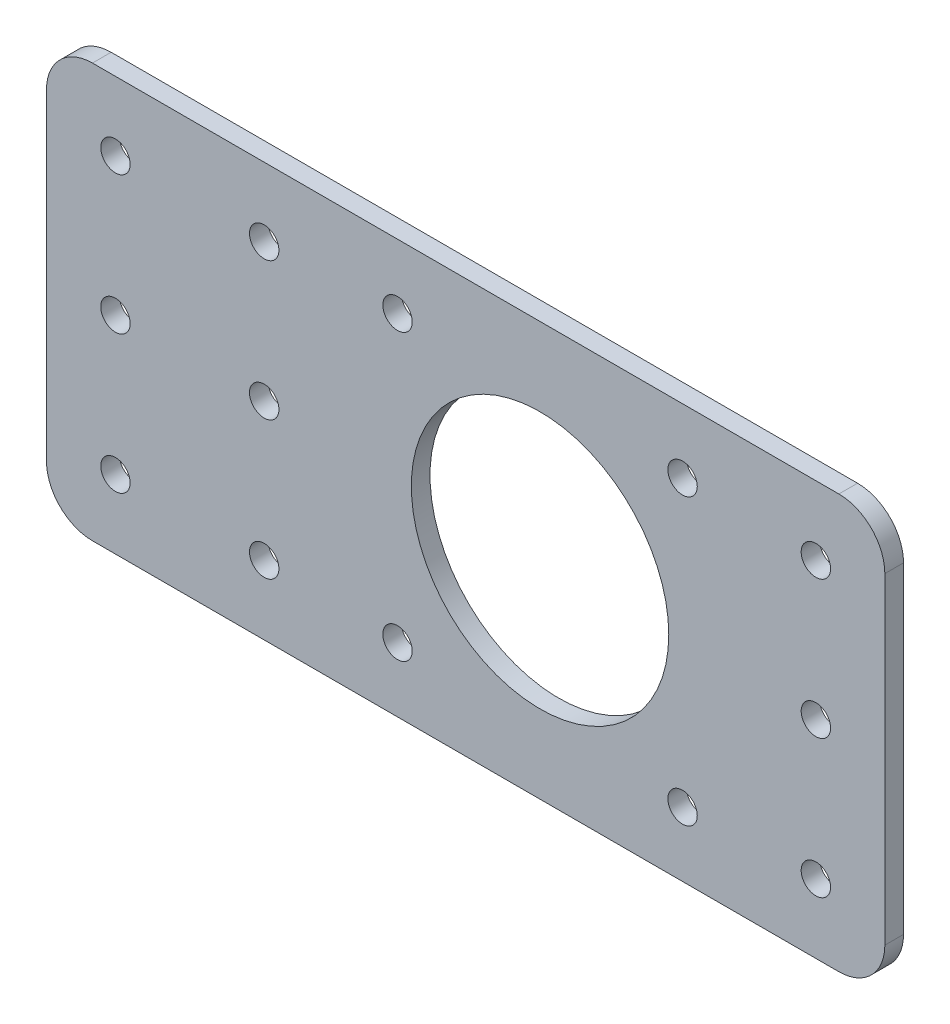
SolidWorks part; units mm, degrees
ref_plane "Front Plane" through (0, 0, 0) normal (0, 0, 1) x (1, 0, 0)
ref_plane "Top Plane" through (0, 0, 0) normal (0, 1, 0) x (1, 0, 0)
ref_plane "Right Plane" through (0, 0, 0) normal (1, 0, 0) x (0, 0, -1)
sketch "Sketch1" plane through (0, 0, 0) normal (0, 0, 1) x (1, 0, 0)
  line L0 (22.5, 22.5) -> (22.5, -22.5) construction
  line L1 (-37.5, -22.5) -> (37.5, -22.5)
  line L2 (-37.5, -22.5) -> (-37.5, 22.5)
  line L3 (-37.5, 22.5) -> (37.5, 22.5)
  line L4 (37.5, -22.5) -> (37.5, 22.5)
  line L5 (-37.5, -22.5) -> (37.5, 22.5) construction
  line L6 (-37.5, 22.5) -> (37.5, -22.5) construction
  line L7 (-15.5, -15.5) -> (15.5, -15.5) construction
  line L8 (-15.5, -15.5) -> (-15.5, 15.5) construction
  line L9 (-15.5, 15.5) -> (15.5, 15.5) construction
  line L10 (15.5, -15.5) -> (15.5, 15.5) construction
  line L11 (-15.5, -15.5) -> (15.5, 15.5) construction
  line L12 (-15.5, 15.5) -> (15.5, -15.5) construction
  line L13 (-22.5, 22.5) -> (-22.5, -22.5) construction
  circle A0 centre (0, 0) radius 14
  circle A1 centre (-15.5, 15.5) radius 1.6
  circle A2 centre (15.5, 15.5) radius 1.6
  circle A3 centre (15.5, -15.5) radius 1.6
  circle A4 centre (-15.5, -15.5) radius 1.6
  point P0 (0, 0)
  dimension "D2" = 28
  dimension "D3" = 3.2
  dimension "D1" = 31
  dimension "D4" = 45
  dimension "D5" = 75
  dimension "D6" = 15
  dimension "D7" = 15
extrude "Boss-Extrude1" add sketch "Sketch1" along normal blind 2.032
fillet "Fillet2" radius 5 4 edges at (37.5, 22.5, 1.016) (37.5, -22.5, 1.016) (-37.5, -22.5, 1.016) (-37.5, 22.5, 1.016)
sketch "Sketch2" plane through (0, 0, 2.032) normal (0, 0, 1) x (1, 0, 0)
  line L0 (0, 40.4519) -> (0, -37.5654) construction
  line L1 (0, -54.6431) -> (0, 54.6431) construction
  line L2 (47.3483, 0) -> (-47.3483, 0) construction
  line L3 (55, 0) -> (-55, 0) construction
  line L4 (-37.5, 17.5) -> (-37.5, -17.5) construction
  circle A0 centre (-30, 0) radius 1.6
  circle A1 centre (-30, 15) radius 1.6
  circle A2 centre (-30, -15) radius 1.6
  circle A3 centre (30, -15) radius 1.6
  circle A4 centre (30, 15) radius 1.6
  circle A5 centre (30, 0) radius 1.6
  dimension "D1" = 3.2
  dimension "D2" = 7.5
  dimension "D3" = 15
extrude "Cut-Extrude1" cut sketch "Sketch2" against normal through all
sketch "Alignment Sketch 1" plane through (0, 0, 2.032) normal (0, 0, 1) x (1, 0, 0)
  line L0 (-30, 15) -> (-30, -15) construction
  line L1 (30, 15) -> (30, -15) construction
  circle A0 centre (30, 15) radius 1.6 construction
  point P0 (-30, 15)
  point P1 (-30, 0)
  point P3 (-30, -15)
  point P5 (30, 15)
  point P7 (30, 0)
  point P8 (30, -15)
sketch "Sketch4" plane through (0, 0, 0) normal (0, 0, -1) x (-1, 0, 0)
  line L1 (53.68, 0) -> (32.5, 0)
  line L2 (53.68, 0) -> (53.68, -22.5)
  line L3 (53.68, -22.5) -> (32.5, -22.5)
  line L4 (32.5, 0) -> (32.5, -22.5)
  line L5 (53.68, 0) -> (32.5, -22.5) construction
  line L6 (53.68, -22.5) -> (32.5, 0) construction
  line L8 (32.5, -22.5) -> (-32.5, -22.5) construction
  line L9 (37.5, 17.5) -> (37.5, -17.5) construction
  point P0 (43.09, -11.25)
  dimension "D1" = 16.18
extrude "Boss-Extrude2" [suppressed] add sketch "Sketch4" against normal up to surface (2.032 mm away)
sketch "Mounting Hole Sketch" [suppressed] plane through (0, 0, 2.032) normal (0, 0, 1) x (1, 0, 0)
  line L0 (-53.68, 0) -> (-53.68, -22.5) construction
  line L1 (-46.18, 0) -> (-46.18, -22.5) construction
  line L2 (-37.5, 0) -> (-53.68, 0) construction
  line L3 (-53.68, -22.5) -> (32.5, -22.5) construction
  circle A0 centre (-46.18, -11.25) radius 1.575
  point P10 (-46.18, -11.25)
  dimension "D2" = 3.15
  dimension "D3" = 7.5
extrude "Mounting Hole Cut" [suppressed] cut sketch "Mounting Hole Sketch" against normal through all
sketch "Sketch5" plane through (0, 0, 2.032) normal (0, 0, 1) x (1, 0, 0)
  line L0 (32.5, 22.5) -> (-32.5, 22.5) construction
  line L1 (-53.68, 22.5) -> (-32.3852, 22.5)
  line L2 (-53.68, 22.5) -> (-53.68, -22.5)
  line L3 (-53.68, -22.5) -> (-32.3852, -22.5)
  line L4 (-32.3852, 22.5) -> (-32.3852, -22.5)
  line L5 (-53.68, 22.5) -> (-32.3852, -22.5) construction
  line L6 (-53.68, -22.5) -> (-32.3852, 22.5) construction
  line L7 (-32.5, -22.5) -> (32.5, -22.5) construction
  line L8 (-37.5, 17.5) -> (-37.5, -17.5) construction
  point P0 (-43.0326, 0)
  dimension "D1" = 16.18
extrude "Boss-Extrude3" add sketch "Sketch5" against normal up to surface (2.032 mm away) up to face at (28.4, 0, 0)
fillet "Fillet3" radius 5 2 edges at (-53.68, -22.5, 1.016) (-53.68, 22.5, 1.016)
sketch "Sketch6" plane through (0, 0, 2.032) normal (0, 0, 1) x (1, 0, 0)
  line L0 (32.5, 22.5) -> (-48.68, 22.5) construction
  line L1 (-53.68, 17.5) -> (-53.68, -17.5) construction
  line L2 (-48.68, -22.5) -> (32.5, -22.5) construction
  line L3 (-53.68, 17.5) -> (-53.68, -17.5) construction
  circle A0 centre (-46.18, 15) radius 1.6
  circle A1 centre (-46.18, 0) radius 1.6
  circle A2 centre (-46.18, -15) radius 1.6
  dimension "D1" = 3.2
  dimension "D2" = 7.5
  dimension "D3" = 7.5
  dimension "D4" = 7.5
  dimension "D5" = 7.5
  dimension "D6" = 7.5
  dimension "D7" = 15
  dimension "D8" = 15
extrude "Cut-Extrude2" cut sketch "Sketch6" against normal through all
